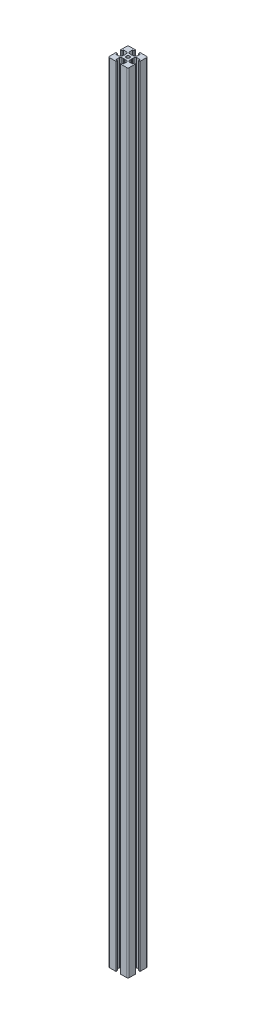
SolidWorks part; units mm, degrees
ref_plane "Front Plane" through (0, 0, 0) normal (0, 0, 1) x (1, 0, 0)
ref_plane "Top Plane" through (0, 0, 0) normal (0, 1, 0) x (1, 0, 0)
ref_plane "Right Plane" through (0, 0, 0) normal (1, 0, 0) x (0, 0, -1)
sketch "Sketch1" plane through (0, 0, 0) normal (0, 1, 0) x (1, 0, 0)
  line L0 (0, 7.5) -> (0, -7.5) construction
  line L1 (6.5, -7.5) -> (1.7, -7.5)
  line L2 (7.5, -6.5) -> (7.5, -1.7)
  line L3 (6.5, 7.5) -> (1.7, 7.5)
  line L4 (-7.5, -6.5) -> (-7.5, -1.7)
  line L5 (7.5, -7.5) -> (-7.5, 7.5) construction
  line L6 (7.5, 7.5) -> (-7.5, -7.5) construction
  line L7 (-1.7, 7.5) -> (-1.7, 6.4)
  line L8 (-1.7, 6.4) -> (-2.85, 6.4)
  line L9 (-2.85, 6.4) -> (-2.85, 3.8)
  line L10 (-1.85, 2.8) -> (-0.5196, 2.8)
  line L11 (-2.85, 3.8) -> (-1.85, 2.8)
  line L12 (0, 2.5) -> (-0.5196, 2.8)
  line L13 (-1.7, 7.5) -> (-6.5, 7.5)
  line L14 (0, 2.5) -> (0.5196, 2.8)
  line L15 (2.85, 3.8) -> (1.85, 2.8)
  line L16 (1.85, 2.8) -> (0.5196, 2.8)
  line L17 (2.85, 6.4) -> (2.85, 3.8)
  line L18 (1.7, 6.4) -> (2.85, 6.4)
  line L19 (1.7, 7.5) -> (1.7, 6.4)
  line L20 (7.5, 1.7) -> (6.4, 1.7)
  line L21 (6.4, 1.7) -> (6.4, 2.85)
  line L22 (6.4, 2.85) -> (3.8, 2.85)
  line L23 (2.8, 1.85) -> (2.8, 0.5196)
  line L24 (3.8, 2.85) -> (2.8, 1.85)
  line L25 (2.5, 0) -> (2.8, 0.5196)
  line L26 (2.5, 0) -> (2.8, -0.5196)
  line L27 (3.8, -2.85) -> (2.8, -1.85)
  line L28 (2.8, -1.85) -> (2.8, -0.5196)
  line L29 (6.4, -2.85) -> (3.8, -2.85)
  line L30 (6.4, -1.7) -> (6.4, -2.85)
  line L31 (7.5, -1.7) -> (6.4, -1.7)
  line L32 (1.7, -7.5) -> (1.7, -6.4)
  line L33 (1.7, -6.4) -> (2.85, -6.4)
  line L34 (2.85, -6.4) -> (2.85, -3.8)
  line L35 (1.85, -2.8) -> (0.5196, -2.8)
  line L36 (2.85, -3.8) -> (1.85, -2.8)
  line L37 (0, -2.5) -> (0.5196, -2.8)
  line L38 (0, -2.5) -> (-0.5196, -2.8)
  line L39 (-2.85, -3.8) -> (-1.85, -2.8)
  line L40 (-1.85, -2.8) -> (-0.5196, -2.8)
  line L41 (-2.85, -6.4) -> (-2.85, -3.8)
  line L42 (-1.7, -6.4) -> (-2.85, -6.4)
  line L43 (-1.7, -7.5) -> (-1.7, -6.4)
  line L44 (-7.5, -1.7) -> (-6.4, -1.7)
  line L45 (-6.4, -1.7) -> (-6.4, -2.85)
  line L46 (-6.4, -2.85) -> (-3.8, -2.85)
  line L47 (-2.8, -1.85) -> (-2.8, -0.5196)
  line L48 (-3.8, -2.85) -> (-2.8, -1.85)
  line L49 (-2.5, 0) -> (-2.8, -0.5196)
  line L50 (-2.5, 0) -> (-2.8, 0.5196)
  line L51 (-3.8, 2.85) -> (-2.8, 1.85)
  line L52 (-2.8, 1.85) -> (-2.8, 0.5196)
  line L53 (-6.4, 2.85) -> (-3.8, 2.85)
  line L54 (-6.4, 1.7) -> (-6.4, 2.85)
  line L55 (-7.5, 1.7) -> (-6.4, 1.7)
  line L56 (7.5, 1.7) -> (7.5, 6.5)
  line L57 (-1.7, -7.5) -> (-6.5, -7.5)
  line L58 (-7.5, 1.7) -> (-7.5, 6.5)
  circle A0 centre (0, 0) radius 1.25
  arc A1 (6.5, -7.5) -> (7.5, -6.5) centre (6.5, -6.5) ccw
  arc A2 (-6.5, -7.5) -> (-7.5, -6.5) centre (-6.5, -6.5) cw
  arc A3 (7.5, 6.5) -> (6.5, 7.5) centre (6.5, 6.5) ccw
  arc A4 (-6.5, 7.5) -> (-7.5, 6.5) centre (-6.5, 6.5) ccw
  point P0 (0, 0)
  point P12 (-2.85, 2.8)
  point P22 (2.85, 2.8)
  point P30 (2.8, 2.85)
  point P40 (2.8, -2.85)
  point P45 (2.85, -2.8)
  point P55 (-2.85, -2.8)
  point P60 (-2.8, -2.85)
  point P70 (-2.8, 2.85)
  point P71 (0, 0)
  dimension "D2" = 2.5
  dimension "D10" = 1
  dimension "D1" = 15
  dimension "D3" = 1.7
  dimension "D4" = 2.85
  dimension "D5" = 1.1
  dimension "D6" = 3.6
  dimension "D7" = 60
  dimension "D8" = 4
extrude "Boss-Extrude1" add sketch "Sketch1" along normal blind 600
